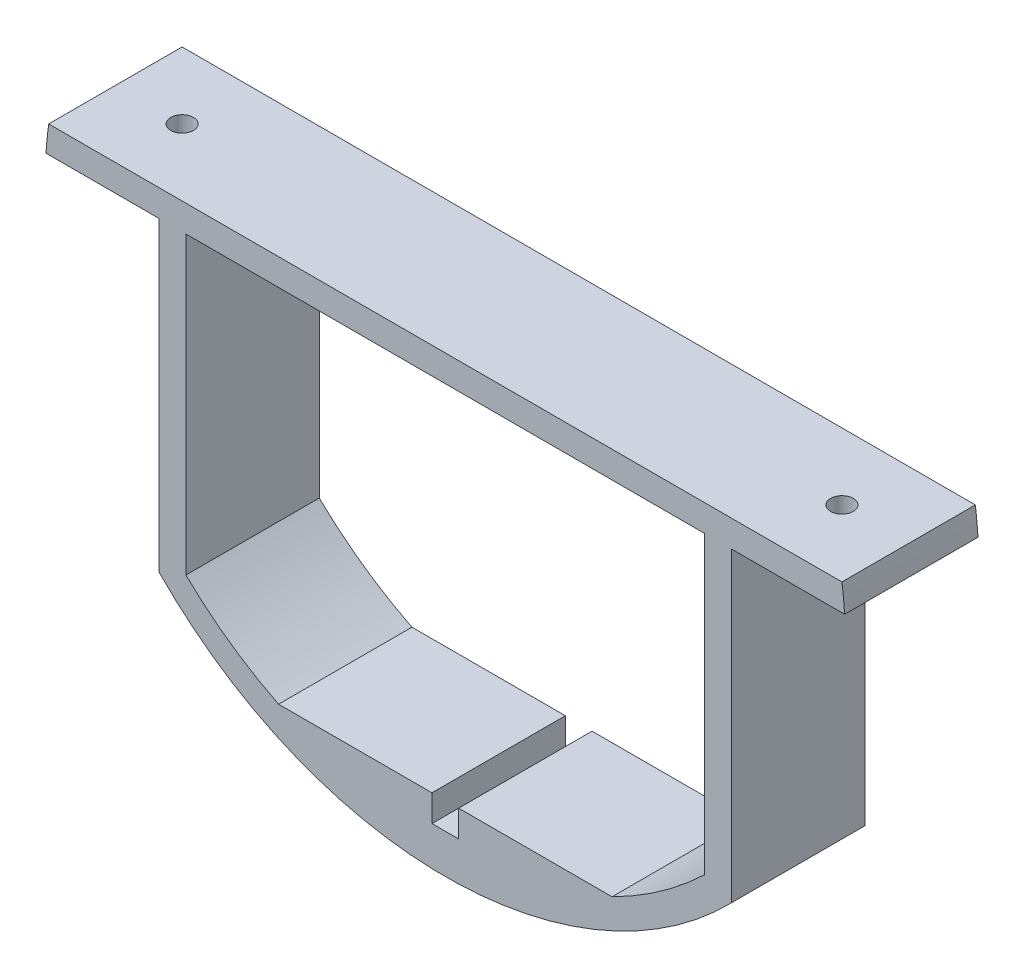
SolidWorks part; units mm, degrees
ref_plane "Front Plane" through (0, 0, 0) normal (0, 0, 1) x (1, 0, 0)
ref_plane "Top Plane" through (0, 0, 0) normal (0, 1, 0) x (1, 0, 0)
ref_plane "Right Plane" through (0, 0, 0) normal (1, 0, 0) x (0, 0, -1)
sketch "Sketch2" plane through (0, 0, 0) normal (0, 0, 1) x (1, 0, 0)
  circle A0 centre (0, 0) radius 76.2
extrude "Boss-Extrude1" add sketch "Sketch2" along normal blind 25.4
sketch "Sketch4" plane through (0, 0, 25.4) normal (0, 0, 1) x (1, 0, 0)
  line L0 (-75.5196, 10.16) -> (75.5196, 10.16)
  circle A0 centre (0, 0) radius 76.2 construction
  arc A1 (-75.5196, 10.16) -> (75.5196, 10.16) centre (0, 0) cw
  dimension "D1" = 10.16
extrude "Cut-Extrude1" cut sketch "Sketch4" against normal blind 76.2
sketch "Sketch5" plane through (0, 0, 25.4) normal (0, 0, 1) x (1, 0, 0)
  line L0 (-70.9383, 5.08) -> (70.9383, 5.08)
  line L1 (-31.75, -63.6395) -> (31.75, -63.6395)
  line L2 (-75.5196, 10.16) -> (75.5196, 10.16) construction
  line L3 (54.4769, 5.08) -> (54.4769, -45.72)
  line L4 (-54.4769, 5.08) -> (-54.4769, -45.72)
  line L5 (49.3969, 5.08) -> (49.3969, -51.1664)
  line L6 (-49.3969, 5.08) -> (-49.3969, -51.1664)
  arc A0 (-70.9383, 5.08) -> (70.9383, 5.08) centre (0, 0) ccw
  arc A1 (-75.5196, 10.16) -> (75.5196, 10.16) centre (0, 0) ccw construction
  point P10 (0, 10.16)
  dimension "D1" = 0
  dimension "D3" = 5.08
  dimension "D2" = 5.08
  dimension "D4" = 63.5
  dimension "D5" = 50.8
  dimension "D6" = 50.8
  dimension "D7" = 5.08
  dimension "D8" = 5.08
extrude "Cut-Extrude2" cut sketch "Sketch5" against normal blind 76.2 contours L0 A0 L1
sketch "Sketch8" plane through (0, 0, 25.4) normal (0, 0, 1) x (1, 0, 0)
  line L0 (-31.75, -63.6395) -> (31.75, -63.6395) construction
  line L1 (-2.54, -63.6395) -> (2.54, -63.6395)
  line L2 (-2.54, -63.6395) -> (-2.54, -68.7195)
  line L3 (-2.54, -68.7195) -> (2.54, -68.7195)
  line L4 (2.54, -63.6395) -> (2.54, -68.7195)
  dimension "D1" = 5.08
  dimension "D2" = 5.08
  dimension "D3" = 29.21
extrude "Cut-Extrude4" cut sketch "Sketch8" against normal blind 50.8
sketch "Sketch9" plane through (0, 0, 25.4) normal (0, 0, 1) x (1, 0, 0)
  line L0 (54.4769, 5.08) -> (76.0305, 5.08)
  line L1 (54.4769, 5.08) -> (54.4769, -53.2795)
  line L2 (49.3969, 5.08) -> (49.3969, -51.1664) construction
  line L3 (-54.4769, 5.08) -> (-54.4769, -53.2795)
  line L4 (-49.3969, 5.08) -> (-49.3969, -51.1664) construction
  line L5 (-54.4769, 5.08) -> (-76.0305, 5.08)
  arc A0 (-75.5196, 10.16) -> (75.5196, 10.16) centre (0, 0) ccw construction
  arc A1 (54.4769, -53.2795) -> (76.0305, 5.08) centre (0, 0) ccw
  arc A2 (-76.0305, 5.08) -> (-54.4769, -53.2795) centre (0, 0) ccw
  dimension "D1" = 5.08
  dimension "D2" = 5.08
extrude "Cut-Extrude5" cut sketch "Sketch9" against normal through all
sketch "Sketch10" plane through (0, 10.16, 0) normal (0, 1, 0) x (1, 0, 0)
  line L0 (-75.5196, 0) -> (75.5196, 0) construction
  line L1 (-75.5196, 0) -> (-75.5196, -25.4) construction
  line L2 (75.5196, 0) -> (75.5196, -25.4) construction
  circle A0 centre (62.8196, -12.7) radius 2.159
  circle A1 centre (-62.8196, -12.7) radius 2.159
  dimension "D1" = 4.318
  dimension "D2" = 12.7
  dimension "D3" = 12.7
  dimension "D4" = 12.7
  dimension "D5" = 12.7
extrude "Cut-Extrude6" cut sketch "Sketch10" against normal blind 25.4
